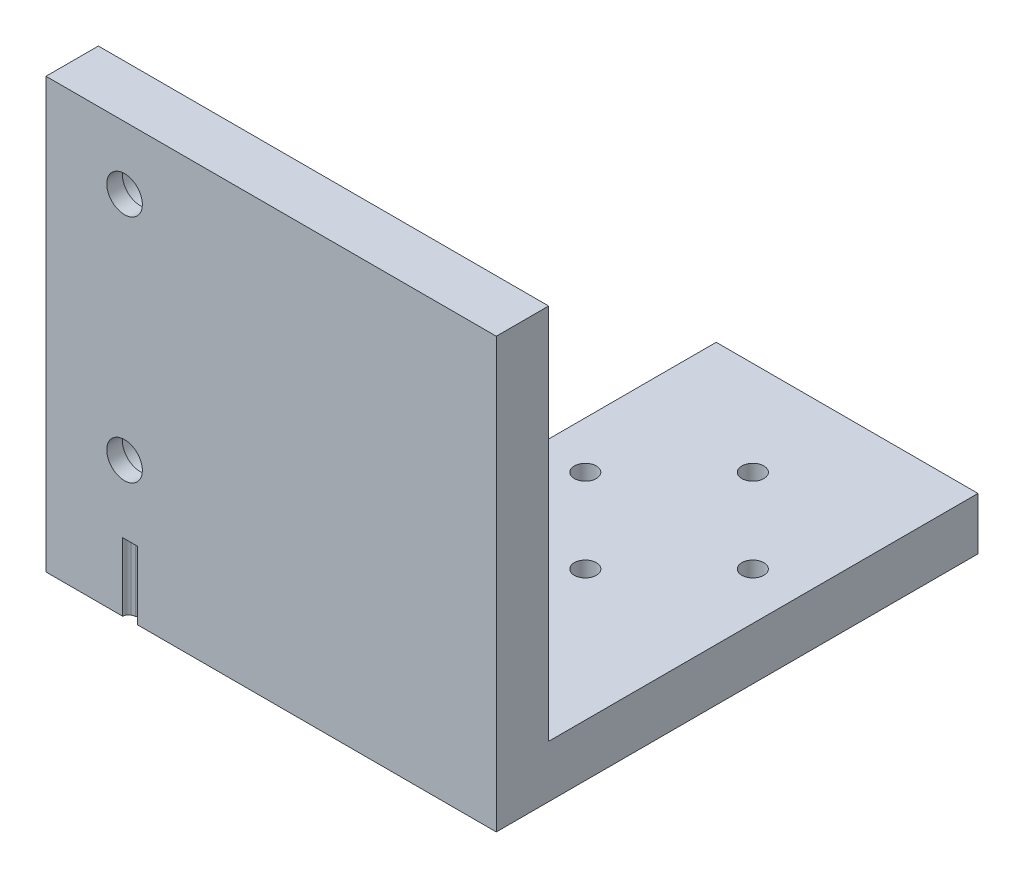
SolidWorks part; units mm, degrees
ref_plane "Front Plane" through (0, 0, 0) normal (0, 0, 1) x (1, 0, 0)
ref_plane "Top Plane" through (0, 0, 0) normal (0, 1, 0) x (1, 0, 0)
ref_plane "Right Plane" through (0, 0, 0) normal (1, 0, 0) x (0, 0, -1)
sketch "Sketch2" plane through (0, 0, 0) normal (0, 1, 0) x (1, 0, 0)
  line L1 (12.5, 17) -> (-12.5, 17)
  line L2 (-12.5, 17) -> (-12.5, -24)
  line L8 (12.5, -24) -> (12.5, 17)
  line L14 (12.5, -24) -> (-12.5, -24)
  arc A2 (0, -6.95) -> (0, -9.05) centre (0, -8) ccw
  arc A3 (0, -9.05) -> (0, -6.95) centre (0, -8) ccw
  arc A6 (-8, 1.05) -> (-8, -1.05) centre (-8, 0) ccw
  arc A7 (-8, -1.05) -> (-8, 1.05) centre (-8, 0) ccw
  arc A8 (8, 1.05) -> (8, -1.05) centre (8, 0) ccw
  arc A9 (8, -1.05) -> (8, 1.05) centre (8, 0) ccw
  arc A12 (0, 6.95) -> (0, 9.05) centre (0, 8) ccw
  arc A13 (0, 9.05) -> (0, 6.95) centre (0, 8) ccw
extrude "Boss-Extrude1" add sketch "Sketch2" along normal blind 5
sketch "Sketch4" plane through (0, 0, 24) normal (0, 0, 1) x (1, 0, 0)
  line L0 (-12.5, 0) -> (12.5, 0)
  line L1 (-12.5, 41) -> (-12.5, 0)
  line L2 (12.5, 0) -> (12.5, 41)
  line L3 (12.5, 41) -> (-12.5, 41)
  point P36 (-12.5, 0)
extrude "Boss-Extrude2" add sketch "Sketch4" along normal blind 5
sketch "Sketch5" plane through (0, 0, 0) normal (0, -1, 0) x (1, 0, 0)
  line L0 (-12.5, 29) -> (-12.5, 24)
  line L1 (-12.5, 29) -> (-30.5, 29)
  line L2 (-30.5, 29) -> (-30.5, 24)
  line L3 (-30.5, 24) -> (-12.5, 24)
  dimension "D1" = 18
extrude "Boss-Extrude3" add sketch "Sketch5" against normal up to surface (41 mm away) contours L0 L3 L2 L1 up to face at (0, 41, 26.5)
sketch "Sketch6" plane through (0, 0, 29) normal (0, 0, 1) x (1, 0, 0)
  line L4 (12.5, 41) -> (-30.5, 41) construction
  circle A0 centre (-23, 13) radius 2.075
  circle A1 centre (-23, 35) radius 2.075
  dimension "D1" = 4.15
  dimension "D2" = 4.15
  dimension "D3" = 6
  dimension "D4" = 22
extrude "Cut-Extrude1" cut sketch "Sketch6" against normal up to surface (5 mm away) up to face at (-10.1667, 15.3333, 24)
sketch "Sketch11" plane through (0, 0, 29) normal (0, 0, 1) x (1, 0, 0)
  circle A4 centre (-23, 13) radius 2.075 construction
  circle A5 centre (-23, 35) radius 2.075 construction
  circle A6 centre (-23, 13) radius 2.075
  circle A7 centre (-23, 35) radius 2.075
  circle A10 centre (-23, 13) radius 1.7
  circle A11 centre (-23, 35) radius 1.7
extrude "Boss-Extrude5" add sketch "Sketch11" against normal blind 1.5
sketch "Sketch12" plane through (0, 0, 0) normal (0, -1, 0) x (1, 0, 0)
  line L0 (-12.5, 18) -> (-12.5, 24)
  line L1 (-12.5, 24) -> (-30.5, 24)
  line L3 (-30.5, 18) -> (-12.5, 18)
  line L6 (-30.5, 24) -> (-30.5, 18)
extrude "Boss-Extrude6" add sketch "Sketch12" against normal blind 5
fillet "Fillet5" radius 2 1 edges at (-30.5, 2.5, 18)
sketch "Sketch13" plane through (0, 0, 0) normal (0, -1, 0) x (-1, 0, 0)
  circle A0 centre (0, -8) radius 2
  circle A1 centre (8, 0) radius 2
  circle A2 centre (0, 8) radius 2
  circle A3 centre (-8, 0) radius 2
extrude "Cut-Extrude2" cut sketch "Sketch13" against normal blind 1.5
sketch "Sketch14" [suppressed] plane through (0, 0, 0) normal (0, -1, 0) x (1, 0, 0)
  line L0 (-22.9641, 29) -> (-22.9641, 18)
  line L1 (-21.9641, 18) -> (-21.9641, 29)
  line L3 (-22.9641, 18) -> (-21.9641, 18)
  line L4 (-21.9641, 29) -> (-22.9641, 29)
sketch "Sketch15" plane through (0, 0, 0) normal (0, -1, 0) x (1, 0, 0)
  line L0 (-21.7446, 29) -> (-21.7446, 18)
  line L1 (-21.7946, 29) -> (-21.7446, 29)
  line L2 (-22.4246, 25.7402) -> (-22.4246, 26.2598)
  line L4 (-22.4246, 23.7402) -> (-22.4246, 24.2598)
  line L5 (-22.4246, 21.7402) -> (-22.4246, 22.2598)
  line L6 (-22.4246, 19.7402) -> (-22.4246, 20.2598)
  line L8 (-21.7946, 29) -> (-23.1746, 29)
  line L10 (-22.4246, 18) -> (-21.7946, 18)
  line L16 (-22.4246, 18) -> (-22.4246, 18.2598)
  line L17 (-22.4246, 28.2598) -> (-22.4246, 27.7402)
  line L21 (-21.7446, 18) -> (-21.7946, 18)
  arc A4 (-22.5551, 19.5915) -> (-22.4246, 19.7402) centre (-22.5746, 19.7402) ccw
  arc A5 (-22.5551, 19.5915) -> (-22.8628, 19.4989) centre (-22.4246, 18.6) ccw
  arc A31 (-22.8628, 18.5011) -> (-22.8628, 19.4989) centre (-22.6196, 19) cw
  arc A32 (-22.5551, 18.4085) -> (-22.8628, 18.5011) centre (-22.4246, 19.4) cw
  arc A33 (-22.5551, 18.4085) -> (-22.4246, 18.2598) centre (-22.5746, 18.2598) cw
  arc A34 (-22.5551, 21.5915) -> (-22.4246, 21.7402) centre (-22.5746, 21.7402) ccw
  arc A35 (-22.5551, 21.5915) -> (-22.8628, 21.4989) centre (-22.4246, 20.6) ccw
  arc A36 (-22.8628, 20.5011) -> (-22.8628, 21.4989) centre (-22.6196, 21) cw
  arc A37 (-22.5551, 20.4085) -> (-22.8628, 20.5011) centre (-22.4246, 21.4) cw
  arc A38 (-22.5551, 20.4085) -> (-22.4246, 20.2598) centre (-22.5746, 20.2598) cw
  arc A39 (-22.5551, 23.5915) -> (-22.4246, 23.7402) centre (-22.5746, 23.7402) ccw
  arc A40 (-22.5551, 23.5915) -> (-22.8628, 23.4989) centre (-22.4246, 22.6) ccw
  arc A41 (-22.8628, 22.5011) -> (-22.8628, 23.4989) centre (-22.6196, 23) cw
  arc A42 (-22.5551, 22.4085) -> (-22.8628, 22.5011) centre (-22.4246, 23.4) cw
  arc A43 (-22.5551, 22.4085) -> (-22.4246, 22.2598) centre (-22.5746, 22.2598) cw
  arc A44 (-22.5551, 25.5915) -> (-22.4246, 25.7402) centre (-22.5746, 25.7402) ccw
  arc A45 (-22.5551, 25.5915) -> (-22.8628, 25.4989) centre (-22.4246, 24.6) ccw
  arc A46 (-22.8628, 24.5011) -> (-22.8628, 25.4989) centre (-22.6196, 25) cw
  arc A47 (-22.5551, 24.4085) -> (-22.8628, 24.5011) centre (-22.4246, 25.4) cw
  arc A48 (-22.5551, 24.4085) -> (-22.4246, 24.2598) centre (-22.5746, 24.2598) cw
  arc A49 (-22.5551, 27.5915) -> (-22.4246, 27.7402) centre (-22.5746, 27.7402) ccw
  arc A50 (-22.5551, 27.5915) -> (-22.8628, 27.4989) centre (-22.4246, 26.6) ccw
  arc A51 (-22.8628, 26.5011) -> (-22.8628, 27.4989) centre (-22.6196, 27) cw
  arc A52 (-22.5551, 26.4085) -> (-22.8628, 26.5011) centre (-22.4246, 27.4) cw
  arc A53 (-22.5551, 26.4085) -> (-22.4246, 26.2598) centre (-22.5746, 26.2598) cw
  arc A54 (-22.5551, 28.4085) -> (-22.4246, 28.2598) centre (-22.5746, 28.2598) cw
  arc A55 (-22.5551, 28.4085) -> (-22.8628, 28.5011) centre (-22.4246, 29.4) cw
  arc A56 (-22.8628, 28.5011) -> (-23.1746, 29) centre (-22.6196, 29) cw
extrude "Cut-Extrude7" cut sketch "Sketch15" against normal blind 6.5
